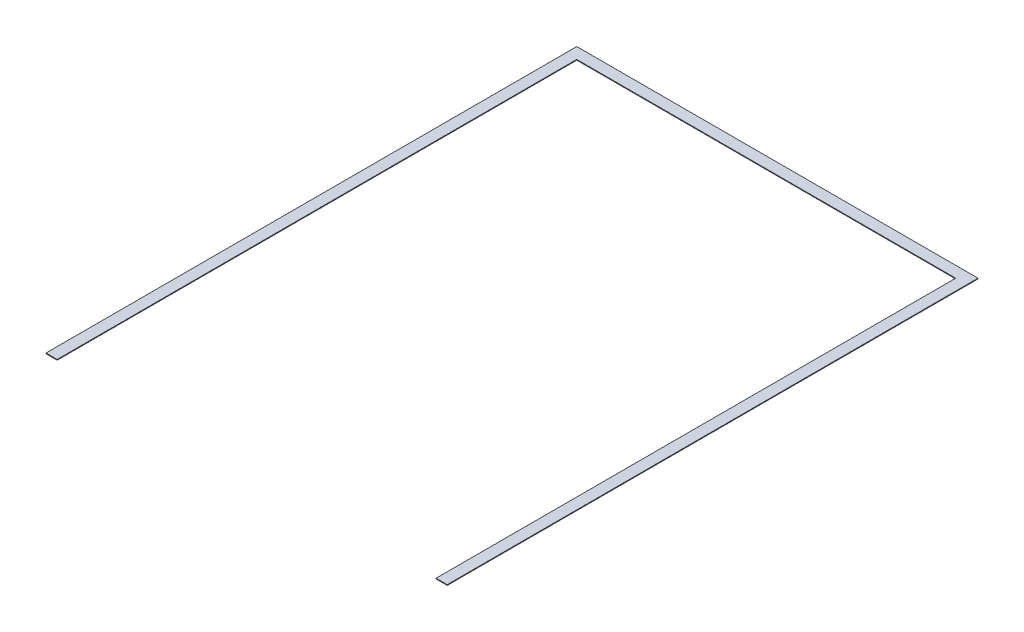
SolidWorks part; units mm, degrees
ref_plane "Front Plane" through (0, 0, 0) normal (0, 0, 1) x (1, 0, 0)
ref_plane "Top Plane" through (0, 0, 0) normal (0, 1, 0) x (1, 0, 0)
ref_plane "Right Plane" through (0, 0, 0) normal (1, 0, 0) x (0, 0, -1)
sketch "Sketch1" plane through (0, 0, 0) normal (0, 1, 0) x (1, 0, 0)
  line L0 (-914.4, -2419.35) -> (-914.4, 0)
  line L1 (-914.4, 0) -> (914.4, 0)
  line L2 (914.4, 0) -> (914.4, -2419.35)
  line L3 (914.4, -2419.35) -> (863.6, -2419.35)
  line L4 (863.6, -2419.35) -> (863.6, -50.8)
  line L5 (863.6, -50.8) -> (-863.6, -50.8)
  line L6 (-863.6, -50.8) -> (-863.6, -2419.35)
  line L7 (-863.6, -2419.35) -> (-914.4, -2419.35)
  dimension "D1" = 1828.8
  dimension "D2" = 2419.35
  dimension "D3" = 50.8
  dimension "D4" = 50.8
  dimension "D5" = 50.8
  dimension "D6" = 914.4
extrude "Boss-Extrude1" add sketch "Sketch1" along normal blind 3.175
